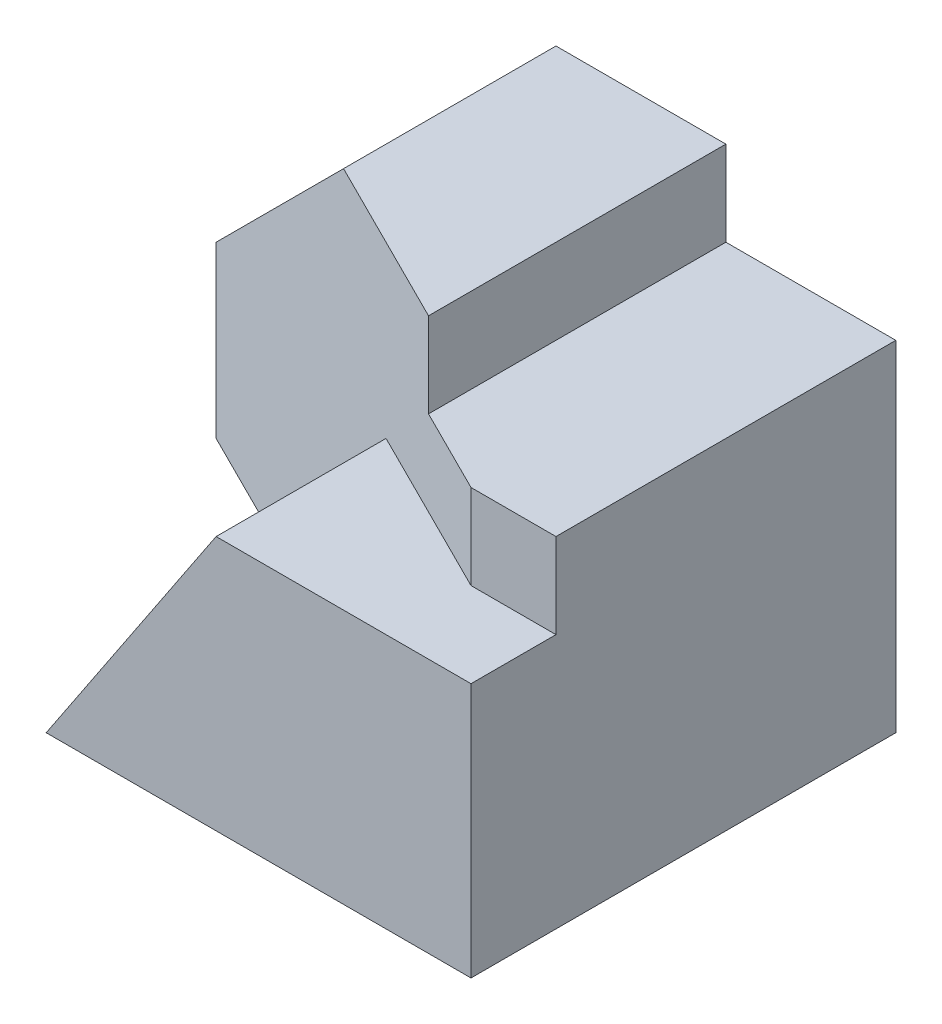
SolidWorks part; units mm, degrees
ref_plane "Front Plane" through (0, 0, 0) normal (0, 0, 1) x (1, 0, 0)
ref_plane "Top Plane" through (0, 0, 0) normal (0, 1, 0) x (1, 0, 0)
ref_plane "Right Plane" through (0, 0, 0) normal (1, 0, 0) x (0, 0, -1)
sketch "Sketch1" plane through (0, 0, 0) normal (0, 0, 1) x (1, 0, 0)
  line L1 (0, 0) -> (70, 0)
  line L2 (0, 0) -> (0, 50)
  line L3 (0, 50) -> (70, 50)
  line L4 (70, 0) -> (70, 50)
  dimension "D1" = 70
  dimension "D2" = 50
extrude "Boss-Extrude1" add sketch "Sketch1" along normal blind 50
sketch "Sketch2" plane through (0, 0, 50) normal (0, 0, 1) x (1, 0, 0)
  line L0 (0, 20) -> (30, 50)
  line L1 (70, 50) -> (50, 50)
  line L2 (70, 50) -> (70, 40)
  line L3 (70, 40) -> (50, 40)
  line L4 (50, 50) -> (50, 40)
  line L5 (0, 50) -> (0, 0) construction
  line L6 (70, 50) -> (0, 50) construction
  line L7 (30, 50) -> (0, 50)
  line L8 (0, 50) -> (0, 20)
  dimension "D1" = 20
  dimension "D2" = 10
  dimension "D3" = 30
  dimension "D4" = 30
extrude "Cut-Extrude1" cut sketch "Sketch2" against normal blind 50
sketch "Sketch3" plane through (0, 0, 0) normal (0, -1, 0) x (1, 0, 0)
  line L0 (0, 10) -> (20, 20)
  line L1 (0, 50) -> (0, 0) construction
  line L2 (20, 20) -> (20, 50)
  line L3 (0, 50) -> (70, 50) construction
  line L4 (20, 50) -> (0, 50)
  line L5 (0, 50) -> (0, 10)
  dimension "D1" = 20
  dimension "D2" = 30
  dimension "D3" = 10
extrude "Cut-Extrude2" cut sketch "Sketch3" against normal blind 50
sketch "Sketch5" plane through (0, 0, 50) normal (0, 0, 1) x (1, 0, 0)
  line L0 (20, 0) -> (40, 30)
  line L1 (40, 30) -> (60, 30)
  line L2 (60, 30) -> (60, 40)
  line L3 (50, 40) -> (70, 40) construction
  line L4 (60, 40) -> (50, 40)
  line L5 (50, 40) -> (50, 50)
  line L6 (50, 50) -> (30, 50)
  line L7 (30, 50) -> (20, 40)
  line L8 (20, 40) -> (20, 0)
  dimension "D1" = 20
  dimension "D2" = 30
  dimension "D3" = 10
extrude "Cut-Extrude3" cut sketch "Sketch5" against normal blind 30
sketch "Sketch6" plane through (0, 0, 50) normal (0, 0, 1) x (1, 0, 0)
  line L1 (60, 30) -> (70, 30)
  line L2 (60, 30) -> (60, 40)
  line L3 (60, 40) -> (70, 40)
  line L4 (70, 30) -> (70, 40)
extrude "Cut-Extrude4" cut sketch "Sketch6" against normal blind 10
sketch "Sketch7" plane through (0, 40, 0) normal (0, 1, 0) x (1, 0, 0)
  line L0 (60, -40) -> (0, -10)
  line L1 (60, -40) -> (60, -20)
  line L2 (0, -10) -> (60, -10)
  line L3 (60, -10) -> (60, -20)
extrude "Boss-Extrude2" add sketch "Sketch7" against normal blind 10
sketch "Sketch8" plane through (0, 0, 10) normal (0, 0, -1) x (-1, 0, 0)
  line L0 (0, 30) -> (-10, 30)
  line L1 (-10, 30) -> (-20, 40)
  line L2 (-20, 40) -> (0, 40)
  line L3 (0, 40) -> (0, 30)
extrude "Cut-Extrude5" cut sketch "Sketch8" against normal blind 10
sketch "Sketch9" plane through (0, 40, 0) normal (0, 1, 0) x (1, 0, 0)
  line L0 (50, -35) -> (30, -25)
  line L1 (50, -20) -> (30, -20)
  line L2 (50, -20) -> (50, -35)
  line L3 (50, -35) -> (30, -35)
  line L4 (30, -20) -> (30, -35)
  line L5 (20, -20) -> (60, -40) construction
  line L6 (30, -25) -> (50, -35)
  line M2 (50, -20) -> (20, -20)
  line M3 (20, -20) -> (60, -40)
  dimension "D1" = 15
  dimension "D2" = 20
extrude "Boss-Extrude3" add sketch "Sketch9" along normal blind 10 contours L4 L2 M2 M3
sketch "Sketch10" plane through (-4, 0, 8) normal (-0.4472, 0, 0.8944) x (0.8944, 0, 0.4472)
  line L0 (26.8328, 40) -> (38.0132, 50)
  line L1 (38.0132, 50) -> (38.0132, 40)
  line L2 (38.0132, 40) -> (26.8328, 40)
extrude "Boss-Extrude4" add sketch "Sketch10" against normal blind 10
sketch "Sketch11" plane through (-10, 10, 0) normal (-0.7071, 0.7071, 0) x (0, 0, 1)
  line L0 (20, 42.4264) -> (20, 56.5685)
  line L1 (20, 56.5685) -> (25, 56.5685)
  line L2 (25, 56.5685) -> (20, 42.4264)
extrude "Boss-Extrude5" add sketch "Sketch11" against normal blind 10
sketch "Sketch12" plane through (-4, 0, 8) normal (-0.4472, 0, 0.8944) x (0.8944, 0, 0.4472)
  line L0 (26.8328, 0) -> (26.8328, 30)
  line L1 (26.8328, 30) -> (49.1935, 30)
  line L2 (49.1935, 30) -> (26.8328, 0)
extrude "Boss-Extrude6" add sketch "Sketch12" against normal blind 22
